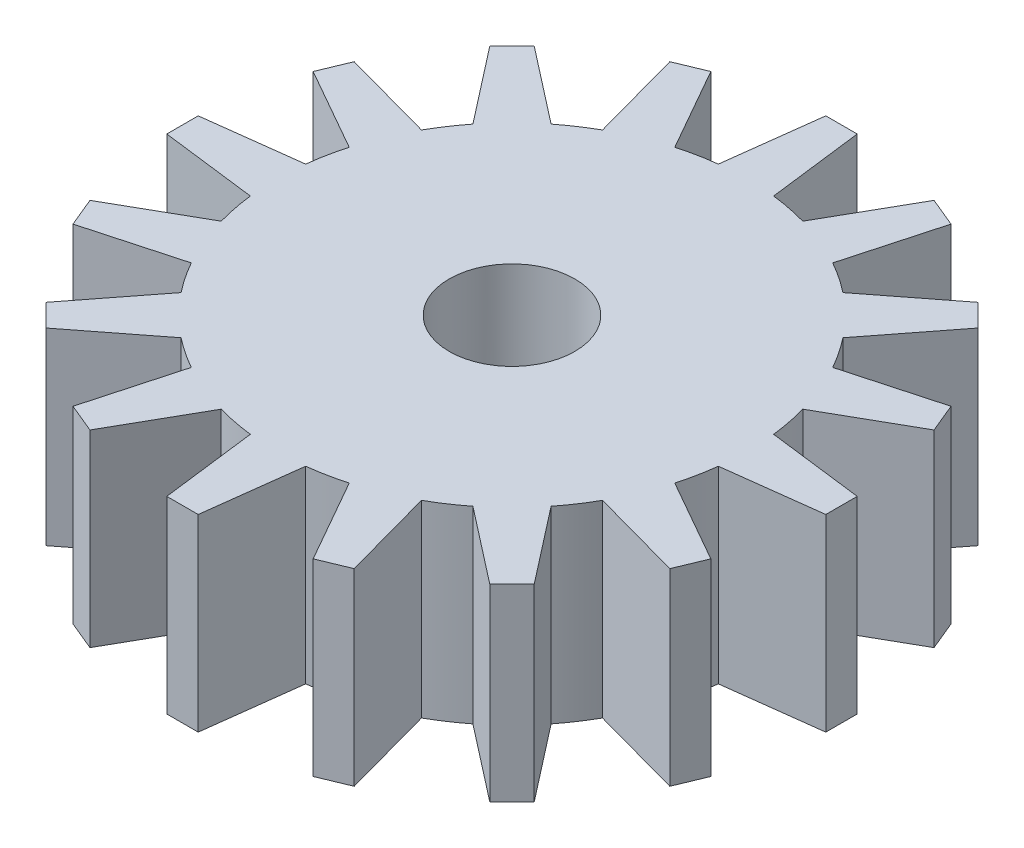
SolidWorks part; units mm, degrees
material "uhlíková ocel 7850"
ref_plane "Přední rovina" through (0, 0, 0) normal (0, 0, 1) x (1, 0, 0)
ref_plane "Horní rovina" through (0, 0, 0) normal (0, 1, 0) x (1, 0, 0)
ref_plane "Pravá rovina" through (0, 0, 0) normal (1, 0, 0) x (0, 0, -1)
sketch "Skica1" plane through (0, 0, 0) normal (0, 1, 0) x (1, 0, 0)
  circle A0 centre (0, 0) radius 3.75
  dimension "D1" = 7.5
extrude "Přidat vysunutím1" add sketch "Skica1" along normal blind 3
sketch "Skica2" plane through (0, 3, 0) normal (0, 1, 0) x (1, 0, 0)
  line L0 (0, 3.75) -> (0, 0) construction
  line L1 (0, 5.244) -> (0.25, 5.244)
  line L2 (0.25, 5.244) -> (0.44, 3.7241)
  line L3 (0, 5.244) -> (0, 3.75) construction
  line L4 (-0.25, 5.244) -> (-0.44, 3.7241)
  line L6 (0, 5.244) -> (-0.25, 5.244)
  circle A0 centre (0, 0) radius 3.75 construction
  arc A1 (-0.44, 3.7241) -> (0.44, 3.7241) centre (0, 0) cw
  circle A2 centre (0, 0) radius 5.25 construction
  dimension "D2" = 10.5
  dimension "D1" = 14.25
  dimension "D3" = 0.5
extrude "Přidat vysunutím2" add sketch "Skica2" against normal up to surface (3 mm away) up to face at (0, 0, 3.75)
pattern_circular "Kruhové pole1" count 16 over 360 about axis through (0, 0, 0) along (0, 1, 0) of "Přidat vysunutím2"
sketch "Skica3" plane through (0, 0, 0) normal (0, -1, 0) x (1, 0, 0)
  circle A0 centre (0, 0) radius 1
  dimension "D1" = 2
extrude "Odebrat vysunutím1" cut sketch "Skica3" against normal blind 5
sketch "Skica4" plane through (0, 0, 0) normal (0, -1, 0) x (1, 0, 0)
  circle A0 centre (0, 0) radius 2.5
  dimension "D1" = 5
extrude "Odebrat vysunutím2" cut sketch "Skica4" against normal blind 1.5
